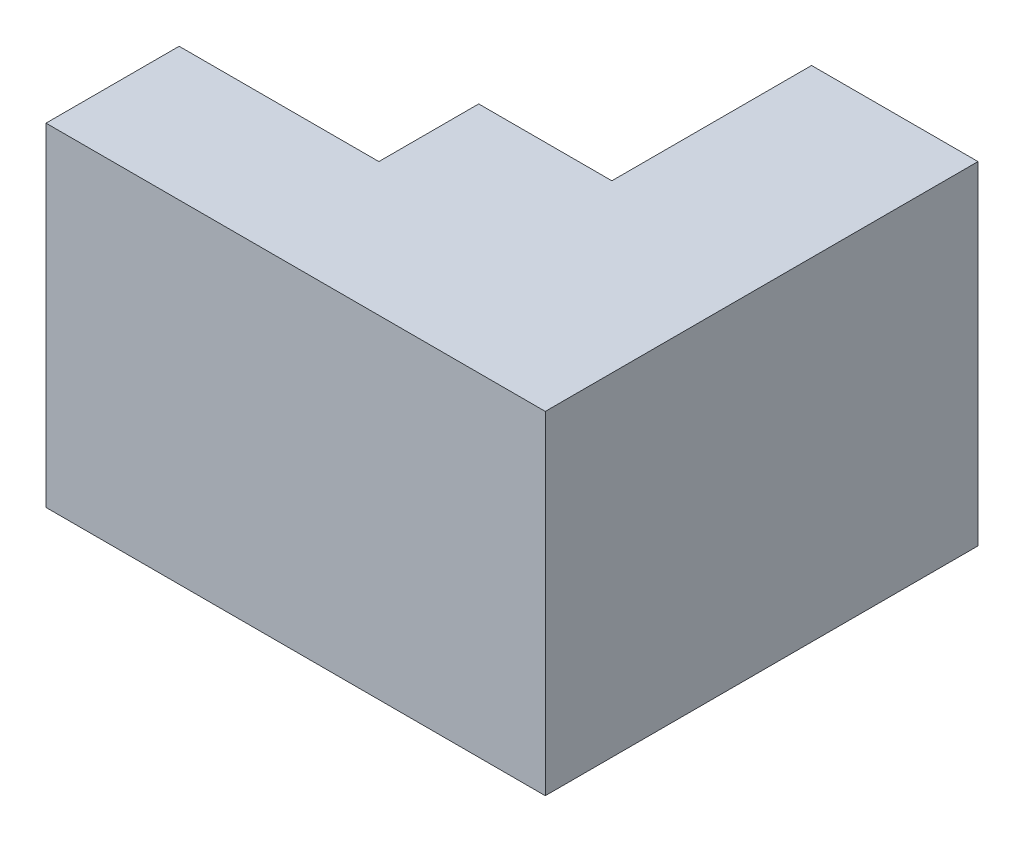
SolidWorks part; units mm, degrees
ref_plane "Front Plane" through (0, 0, 0) normal (0, 0, 1) x (1, 0, 0)
ref_plane "Top Plane" through (0, 0, 0) normal (0, 1, 0) x (1, 0, 0)
ref_plane "Right Plane" through (0, 0, 0) normal (1, 0, 0) x (0, 0, -1)
sketch "Sketch1" plane through (0, 0, 0) normal (0, 1, 0) x (1, 0, 0)
  line L0 (0, 0) -> (75, 0)
  line L1 (75, 0) -> (75, 65)
  line L2 (75, 65) -> (50, 65)
  line L3 (50, 65) -> (50, 35)
  line L4 (50, 35) -> (30, 35)
  line L5 (30, 35) -> (30, 20)
  line L6 (30, 20) -> (0, 20)
  line L7 (0, 20) -> (0, 0)
  dimension "D1" = 75
  dimension "D2" = 20
  dimension "D3" = 15
  dimension "D4" = 30
  dimension "D5" = 30
  dimension "D6" = 20
  dimension "D7" = 25
extrude "Boss-Extrude1" add sketch "Sketch1" along normal blind 50
